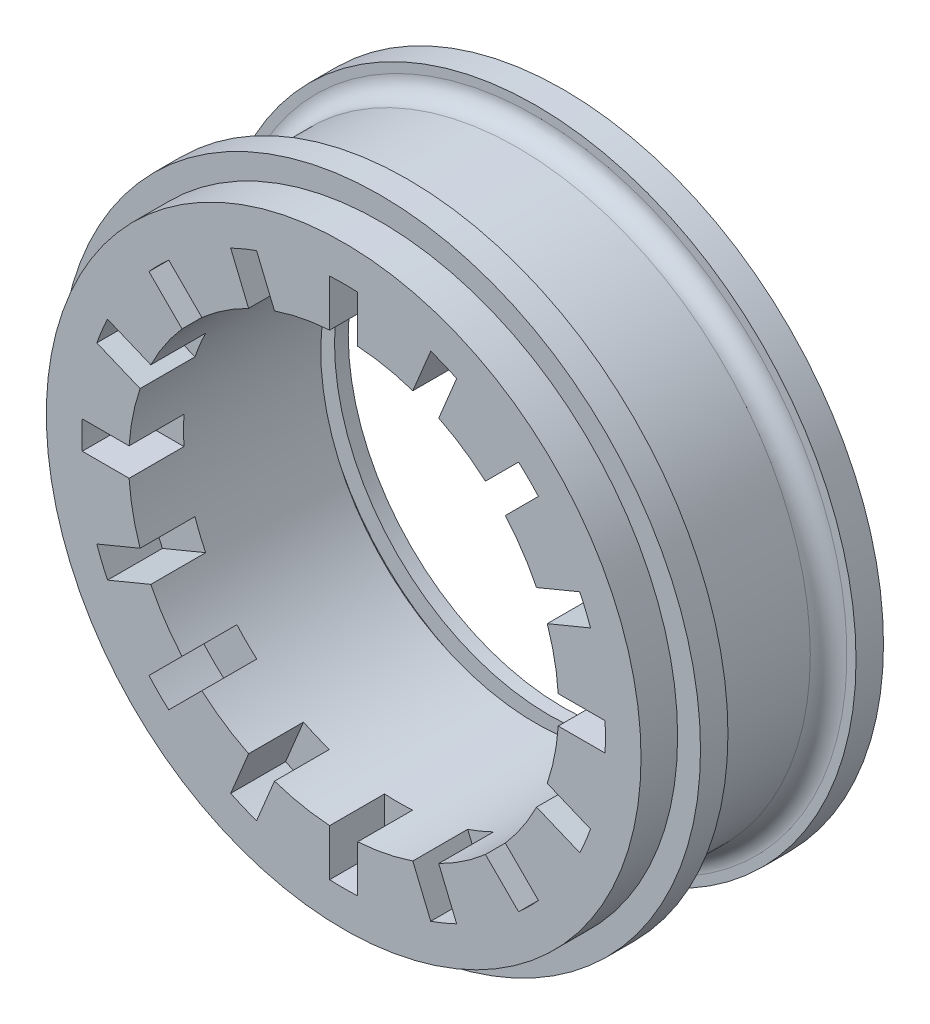
SolidWorks part; units mm, degrees
ref_plane "前视基准面" through (0, 0, 0) normal (0, 0, 1) x (1, 0, 0)
ref_plane "上视基准面" through (0, 0, 0) normal (0, 1, 0) x (1, 0, 0)
ref_plane "右视基准面" through (0, 0, 0) normal (1, 0, 0) x (0, 0, -1)
sketch "草图1" plane through (0, 0, 0) normal (0, 0, 1) x (1, 0, 0)
  line L1 (0, 25) -> (0, -25) construction
  line L2 (0, 0) -> (-25, 0) construction
  line L3 (0, 0) -> (25, 0) construction
  circle A0 centre (0, 0) radius 23.5
  circle A1 centre (0, 0) radius 25
  circle A2 centre (0, 0) radius 35
extrude "凸台-拉伸1" add sketch "草图1" along normal mid plane 20 contours A1 A0 | A2 A1
sketch "草图2" plane through (0, 0, 0) normal (1, 0, 0) x (0, 0, -1)
  line L4 (-7, 40) -> (-7, 34)
  line L6 (-5, 32) -> (5, 32)
  line L7 (7, 34) -> (7, 40)
  line L8 (0, 0) -> (-10, 0) construction
  line L9 (-7, 40) -> (7, 40)
  arc A0 (5, 32) -> (7, 34) centre (5, 34) ccw
  arc A1 (-5, 32) -> (-7, 34) centre (-5, 34) cw
  point P0 (0, 40)
revolve "切除-旋转1" cut sketch "草图2" angle 360 about L8
ref_plane "基准面1" through (0, 0, 10) normal (0, 0, 1) x (1, 0, 0)
sketch "草图3" plane through (0, 0, 10) normal (0, 0, 1) x (1, 0, 0)
  circle A0 centre (0, 0) radius 23.5
  circle A1 centre (0, 0) radius 32.5
extrude "凸台-拉伸2" add sketch "草图3" along normal blind 4
ref_plane "基准面2" through (0, 0, 14) normal (0, 0, 1) x (1, 0, 0)
sketch "草图5" plane through (0, 0, 14) normal (0, 0, 1) x (1, 0, 0)
  line L0 (0, 28.6087) -> (0, -28.6087) construction
  line L1 (-28.6087, 0) -> (28.6087, 0) construction
  line L2 (0, 0) -> (-8.8687, 8.8687) construction
  line L3 (-8.8687, 8.8687) -> (-20.2294, 20.2294) construction
  line L4 (0, 0) -> (20.2294, -20.2294) construction
  line L5 (0, 0) -> (-20.2294, -20.2294) construction
  line L6 (0, 0) -> (20.2294, 20.2294) construction
  line L7 (0, 23.5) -> (0, 26.042) construction
  line L8 (8.5499, 24.6461) -> (7.558, 22.2515)
  line L9 (11.3818, 23.4731) -> (10.3899, 21.0784)
  line L10 (-1.5326, 26.042) -> (-1.5326, 23.45)
  line L11 (1.5326, 26.042) -> (1.5326, 23.45)
  line L12 (-1.5326, 26.042) -> (-1.5326, 28.5676)
  line L13 (1.5326, 26.042) -> (1.5326, 28.5676)
  line L14 (8.5499, 24.6461) -> (9.5164, 26.9795)
  line L15 (11.3818, 23.4731) -> (12.3483, 25.8065)
  line L16 (10.9481, 26.431) -> (-10.9481, -26.431) construction
  line L17 (8.9931, 21.7112) -> (9.9658, 24.0596) construction
  line L18 (17.3307, 19.4982) -> (15.4979, 17.6654)
  line L19 (19.4982, 17.3307) -> (17.6654, 15.4979)
  line L20 (17.3307, 19.4982) -> (19.1166, 21.2841)
  line L21 (19.4982, 17.3307) -> (21.2841, 19.1166)
  line L22 (20.2294, 20.2294) -> (-20.2294, -20.2294) construction
  line L23 (16.617, 16.617) -> (18.4144, 18.4144) construction
  line L24 (23.4731, 11.3818) -> (21.0784, 10.3899)
  line L25 (24.6461, 8.5499) -> (22.2515, 7.558)
  line L26 (23.4731, 11.3818) -> (25.8065, 12.3483)
  line L27 (24.6461, 8.5499) -> (26.9795, 9.5164)
  line L28 (26.431, 10.9481) -> (-26.431, -10.9481) construction
  line L29 (21.7112, 8.9931) -> (24.0596, 9.9658) construction
  line L30 (26.042, 1.5326) -> (23.45, 1.5326)
  line L31 (26.042, -1.5326) -> (23.45, -1.5326)
  line L32 (26.042, 1.5326) -> (28.5676, 1.5326)
  line L33 (26.042, -1.5326) -> (28.5676, -1.5326)
  line L34 (28.6087, 0) -> (-28.6087, 0) construction
  line L35 (23.5, 0) -> (26.042, 0) construction
  line L36 (24.6461, -8.5499) -> (22.2515, -7.558)
  line L37 (23.4731, -11.3818) -> (21.0784, -10.3899)
  line L38 (24.6461, -8.5499) -> (26.9795, -9.5164)
  line L39 (23.4731, -11.3818) -> (25.8065, -12.3483)
  line L40 (26.431, -10.9481) -> (-26.431, 10.9481) construction
  line L41 (21.7112, -8.9931) -> (24.0596, -9.9658) construction
  line L42 (19.4982, -17.3307) -> (17.6654, -15.4979)
  line L43 (17.3307, -19.4982) -> (15.4979, -17.6654)
  line L44 (19.4982, -17.3307) -> (21.2841, -19.1166)
  line L45 (17.3307, -19.4982) -> (19.1166, -21.2841)
  line L46 (20.2294, -20.2294) -> (-20.2294, 20.2294) construction
  line L47 (16.617, -16.617) -> (18.4144, -18.4144) construction
  line L48 (11.3818, -23.4731) -> (10.3899, -21.0784)
  line L49 (8.5499, -24.6461) -> (7.558, -22.2515)
  line L50 (11.3818, -23.4731) -> (12.3483, -25.8065)
  line L51 (8.5499, -24.6461) -> (9.5164, -26.9795)
  line L52 (10.9481, -26.431) -> (-10.9481, 26.431) construction
  line L53 (8.9931, -21.7112) -> (9.9658, -24.0596) construction
  line L54 (1.5326, -26.042) -> (1.5326, -23.45)
  line L55 (-1.5326, -26.042) -> (-1.5326, -23.45)
  line L56 (1.5326, -26.042) -> (1.5326, -28.5676)
  line L57 (-1.5326, -26.042) -> (-1.5326, -28.5676)
  line L58 (0, -28.6087) -> (0, 28.6087) construction
  line L59 (0, -23.5) -> (0, -26.042) construction
  line L60 (-8.5499, -24.6461) -> (-7.558, -22.2515)
  line L61 (-11.3818, -23.4731) -> (-10.3899, -21.0784)
  line L62 (-8.5499, -24.6461) -> (-9.5164, -26.9795)
  line L63 (-11.3818, -23.4731) -> (-12.3483, -25.8065)
  line L64 (-10.9481, -26.431) -> (10.9481, 26.431) construction
  line L65 (-8.9931, -21.7112) -> (-9.9658, -24.0596) construction
  line L66 (-17.3307, -19.4982) -> (-15.4979, -17.6654)
  line L67 (-19.4982, -17.3307) -> (-17.6654, -15.4979)
  line L68 (-17.3307, -19.4982) -> (-19.1166, -21.2841)
  line L69 (-19.4982, -17.3307) -> (-21.2841, -19.1166)
  line L70 (-20.2294, -20.2294) -> (20.2294, 20.2294) construction
  line L71 (-16.617, -16.617) -> (-18.4144, -18.4144) construction
  line L72 (-23.4731, -11.3818) -> (-21.0784, -10.3899)
  line L73 (-24.6461, -8.5499) -> (-22.2515, -7.558)
  line L74 (-23.4731, -11.3818) -> (-25.8065, -12.3483)
  line L75 (-24.6461, -8.5499) -> (-26.9795, -9.5164)
  line L76 (-26.431, -10.9481) -> (26.431, 10.9481) construction
  line L77 (-21.7112, -8.9931) -> (-24.0596, -9.9658) construction
  line L78 (-26.042, -1.5326) -> (-23.45, -1.5326)
  line L79 (-26.042, 1.5326) -> (-23.45, 1.5326)
  line L80 (-26.042, -1.5326) -> (-28.5676, -1.5326)
  line L81 (-26.042, 1.5326) -> (-28.5676, 1.5326)
  line L82 (-28.6087, 0) -> (28.6087, 0) construction
  line L83 (-23.5, 0) -> (-26.042, 0) construction
  line L84 (-24.6461, 8.5499) -> (-22.2515, 7.558)
  line L85 (-23.4731, 11.3818) -> (-21.0784, 10.3899)
  line L86 (-24.6461, 8.5499) -> (-26.9795, 9.5164)
  line L87 (-23.4731, 11.3818) -> (-25.8065, 12.3483)
  line L88 (-26.431, 10.9481) -> (26.431, -10.9481) construction
  line L89 (-21.7112, 8.9931) -> (-24.0596, 9.9658) construction
  line L90 (-19.4982, 17.3307) -> (-17.6654, 15.4979)
  line L91 (-17.3307, 19.4982) -> (-15.4979, 17.6654)
  line L92 (-19.4982, 17.3307) -> (-21.2841, 19.1166)
  line L93 (-17.3307, 19.4982) -> (-19.1166, 21.2841)
  line L94 (-20.2294, 20.2294) -> (20.2294, -20.2294) construction
  line L95 (-16.617, 16.617) -> (-18.4144, 18.4144) construction
  line L96 (-11.3818, 23.4731) -> (-10.3899, 21.0784)
  line L97 (-8.5499, 24.6461) -> (-7.558, 22.2515)
  line L98 (-11.3818, 23.4731) -> (-12.3483, 25.8065)
  line L99 (-8.5499, 24.6461) -> (-9.5164, 26.9795)
  line L100 (-10.9481, 26.431) -> (10.9481, -26.431) construction
  line L101 (-8.9931, 21.7112) -> (-9.9658, 24.0596) construction
  arc A0 (7.558, 22.2515) -> (10.3734, 21.0866) centre (0, 0) cw
  arc A1 (9.5164, 26.9795) -> (12.3483, 25.8065) centre (0, 0) cw
  arc A2 (-1.5326, 23.45) -> (1.5143, 23.4512) centre (0, 0) cw
  arc A3 (-1.5326, 28.5676) -> (1.5326, 28.5676) centre (0, 0) cw
  arc A4 (15.4979, 17.6654) -> (17.6532, 15.5117) centre (0, 0) cw
  arc A5 (19.1166, 21.2841) -> (21.2841, 19.1166) centre (0, 0) cw
  arc A6 (21.0784, 10.3899) -> (22.2455, 7.5753) centre (0, 0) cw
  arc A7 (25.8065, 12.3483) -> (26.9795, 9.5164) centre (0, 0) cw
  arc A8 (23.45, 1.5326) -> (23.4512, -1.5143) centre (0, 0) cw
  arc A9 (28.5676, 1.5326) -> (28.5676, -1.5326) centre (0, 0) cw
  arc A10 (22.2515, -7.558) -> (21.0866, -10.3734) centre (0, 0) cw
  arc A11 (26.9795, -9.5164) -> (25.8065, -12.3483) centre (0, 0) cw
  arc A12 (17.6654, -15.4979) -> (15.5117, -17.6532) centre (0, 0) cw
  arc A13 (21.2841, -19.1166) -> (19.1166, -21.2841) centre (0, 0) cw
  arc A14 (10.3899, -21.0784) -> (7.5753, -22.2455) centre (0, 0) cw
  arc A15 (12.3483, -25.8065) -> (9.5164, -26.9795) centre (0, 0) cw
  arc A16 (-1.5326, 28.5676) -> (-19.1166, 21.2841) centre (0, 0) ccw
  arc A17 (19.1166, 21.2841) -> (1.5326, 28.5676) centre (0, 0) ccw
  arc A18 (28.5676, 1.5326) -> (21.2841, 19.1166) centre (0, 0) ccw
  arc A19 (21.2841, -19.1166) -> (28.5676, -1.5326) centre (0, 0) ccw
  arc A20 (1.5326, -28.5676) -> (19.1166, -21.2841) centre (0, 0) ccw
  arc A21 (-19.1166, -21.2841) -> (-1.5326, -28.5676) centre (0, 0) ccw
  arc A22 (-28.5676, -1.5326) -> (-21.2841, -19.1166) centre (0, 0) ccw
  arc A23 (-21.2841, 19.1166) -> (-28.5676, 1.5326) centre (0, 0) ccw
  circle A24 centre (0, 0) radius 23.5
  arc A25 (1.5326, -23.45) -> (-1.5143, -23.4512) centre (0, 0) cw
  arc A26 (1.5326, -28.5676) -> (-1.5326, -28.5676) centre (0, 0) cw
  arc A27 (-7.558, -22.2515) -> (-10.3734, -21.0866) centre (0, 0) cw
  arc A28 (-9.5164, -26.9795) -> (-12.3483, -25.8065) centre (0, 0) cw
  arc A29 (-15.4979, -17.6654) -> (-17.6532, -15.5117) centre (0, 0) cw
  arc A30 (-19.1166, -21.2841) -> (-21.2841, -19.1166) centre (0, 0) cw
  arc A31 (-21.0784, -10.3899) -> (-22.2455, -7.5753) centre (0, 0) cw
  arc A32 (-25.8065, -12.3483) -> (-26.9795, -9.5164) centre (0, 0) cw
  arc A33 (-23.45, -1.5326) -> (-23.4512, 1.5143) centre (0, 0) cw
  arc A34 (-28.5676, -1.5326) -> (-28.5676, 1.5326) centre (0, 0) cw
  arc A35 (-22.2515, 7.558) -> (-21.0866, 10.3734) centre (0, 0) cw
  arc A36 (-26.9795, 9.5164) -> (-25.8065, 12.3483) centre (0, 0) cw
  arc A37 (-17.6654, 15.4979) -> (-15.5117, 17.6532) centre (0, 0) cw
  arc A38 (-21.2841, 19.1166) -> (-19.1166, 21.2841) centre (0, 0) cw
  arc A39 (-10.3899, 21.0784) -> (-7.5753, 22.2455) centre (0, 0) cw
  arc A40 (-12.3483, 25.8065) -> (-9.5164, 26.9795) centre (0, 0) cw
  point P99 (0, 0)
  point P114 (0, 0)
  dimension "D1" = 16
  dimension "D2" = 8
extrude "切除-拉伸1" cut sketch "草图5" against normal blind 6 contours A24 L43 L45 A13 L44 L42 A12 | A24 L37 L39 A11 L38 L36 A10 | A24 L31 L33 A9 L32 L30 A8 | A24 L25 L27 A7 L26 L24 A6 | A24 L19 L21 A5 L20 L18 A4 | A24 L9 L15 A1 L14 L8 A0 | A24 L11 L13 A3 L12 L10 A2 | A24 L49 L51 A15 L50 L48 A14 | A26 L56 L54 A24 L55 L57 | A24 L61 L63 A21 L62 L60 | A30 L68 L66 A24 L67 L69 | A24 L73 L75 A22 L74 L72 | A34 L80 L78 A24 L79 L81 | A24 L85 L87 A23 L86 L84 | A38 L92 L90 A24 L91 L93 | A24 L97 L99 A16 L98 L96
ref_plane "基准面3" through (0, 0, 7) normal (0, 0, -1) x (-1, 0, 0)
sketch "草图6" plane through (0, 0, 7) normal (0, 0, -1) x (-1, 0, 0)
  circle A0 centre (0, 0) radius 23.5
  circle A1 centre (0, 0) radius 21.5
sketch "草图7" plane through (0, 0, 0) normal (1, 0, 0) x (0, 0, -1)
  line L0 (0, 0) -> (10, 0) construction
  line L1 (7, 25.5) -> (8.5, 25.5)
  line L2 (7, 25.5) -> (7, 23.5)
  line L3 (8.5, 23.5) -> (8.5, 25.5)
  line L4 (8.5, 23.5) -> (7, 23.5)
revolve "切除-旋转2" cut sketch "草图7" angle 360 about L0
